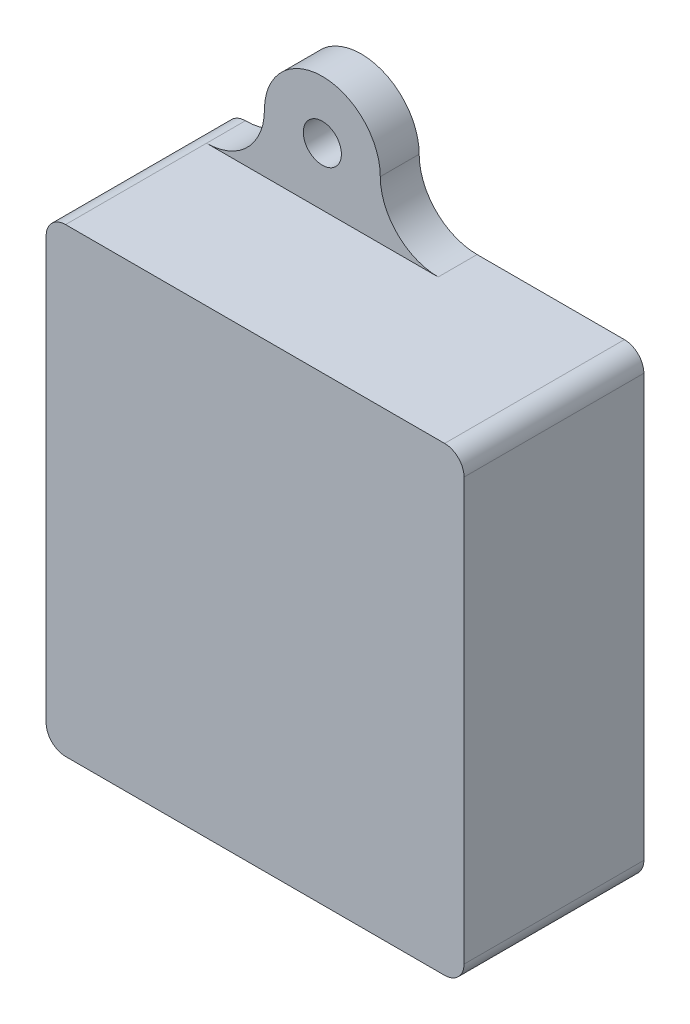
SolidWorks part; units mm, degrees
ref_plane "Front Plane" through (0, 0, 0) normal (0, 0, 1) x (1, 0, 0)
ref_plane "Top Plane" through (0, 0, 0) normal (0, 1, 0) x (1, 0, 0)
ref_plane "Right Plane" through (0, 0, 0) normal (1, 0, 0) x (0, 0, -1)
sketch "Sketch1" plane through (0, 0, 0) normal (0, 0, 1) x (1, 0, 0)
  line L1 (2.54, 0) -> (52.07, 0)
  line L2 (0, 2.54) -> (0, 57.658)
  line L3 (2.54, 60.198) -> (52.07, 60.198)
  line L4 (54.61, 2.54) -> (54.61, 57.658)
  arc A0 (2.54, 0) -> (0, 2.54) centre (2.54, 2.54) cw
  arc A1 (52.07, 0) -> (54.61, 2.54) centre (52.07, 2.54) ccw
  arc A2 (52.07, 60.198) -> (54.61, 57.658) centre (52.07, 57.658) cw
  arc A3 (0, 57.658) -> (2.54, 60.198) centre (2.54, 57.658) cw
  point P7 (0, 0)
  point P10 (54.61, 0)
  point P15 (0, 60.198)
  dimension "D3" = 2.54
  dimension "D1" = 54.61
  dimension "D2" = 60.198
extrude "Boss-Extrude1" add sketch "Sketch1" along normal blind 23.495 contours L2 A3 L3 A2 L4 A1 L1 A0
shell "Shell1" thickness 3.429
fillet "Fillet1" radius 2.54 4 edges at (3.429, 56.769, 10.033) (3.429, 3.429, 10.033) (51.181, 3.429, 10.033) (51.181, 56.769, 10.033)
sketch "Sketch2" plane through (0, 0, 0) normal (0, 0, -1) x (-1, 0, 0)
  line L0 (-2.54, 0) -> (-52.07, 0) construction
  line L1 (-2.54, 60.198) -> (-52.07, 60.198) construction
  circle A0 centre (-17.6784, -7.5692) radius 2.4892
  circle A1 centre (-17.6784, -7.5692) radius 7.5692
  arc A2 (-10.1092, -7.5692) -> (-2.54, 0) centre (-2.54, -7.5692) cw
  arc A3 (-25.2476, -7.5692) -> (-32.8168, 0) centre (-32.8168, -7.5692) ccw
  arc A4 (-25.2476, -7.5692) -> (-32.8168, 0) centre (-32.8168, -7.5692) ccw construction
  circle A5 centre (-17.6784, 67.7672) radius 2.4892
  circle A6 centre (-17.6784, 67.7672) radius 7.5692
  arc A7 (-10.1092, 67.7672) -> (-2.54, 60.198) centre (-2.54, 67.7672) ccw
  arc A8 (-25.2476, 67.7672) -> (-32.8168, 60.198) centre (-32.8168, 67.7672) cw
  arc A9 (-32.8168, 60.198) -> (-25.2476, 67.7672) centre (-32.8168, 67.7672) ccw construction
  line M5 (-2.54, 60.198) -> (-52.07, 60.198)
  line M9 (-52.07, 0) -> (-2.54, 0)
  dimension "D1" = 4.9784
  dimension "D2" = 5.08
extrude "Boss-Extrude2" add sketch "Sketch2" against normal blind 5.08 contours A6 A8 M5 | A6 A5 | A7 A6 M5 | A1 A0 | A3 A1 M9 | A1 A2 M9
sketch "Sketch3" plane through (0, 0, 0) normal (-1, 0, 0) x (0, 0, 1)
  line L0 (0, 2.54) -> (0, 57.658) construction
  line L1 (0, 46.3042) -> (3.81, 46.3042)
  line L2 (0, 46.3042) -> (0, 5.969)
  line L3 (0, 5.969) -> (3.81, 5.969)
  line L4 (3.81, 46.3042) -> (3.81, 5.969)
  line L5 (23.495, 57.658) -> (0, 57.658) construction
  line L6 (23.495, 2.54) -> (0, 2.54) construction
  point P8 (1.905, 5.969)
  dimension "D1" = 11.3538
  dimension "D2" = 3.429
  dimension "D3" = 3.81
extrude "Cut-Extrude1" cut sketch "Sketch3" against normal up to next
fillet "Fillet2" radius 1.27 4 edges at (3.429, 46.3042, 1.905) (0, 46.3042, 1.905) (0, 5.969, 1.905) (3.429, 5.969, 1.905)
